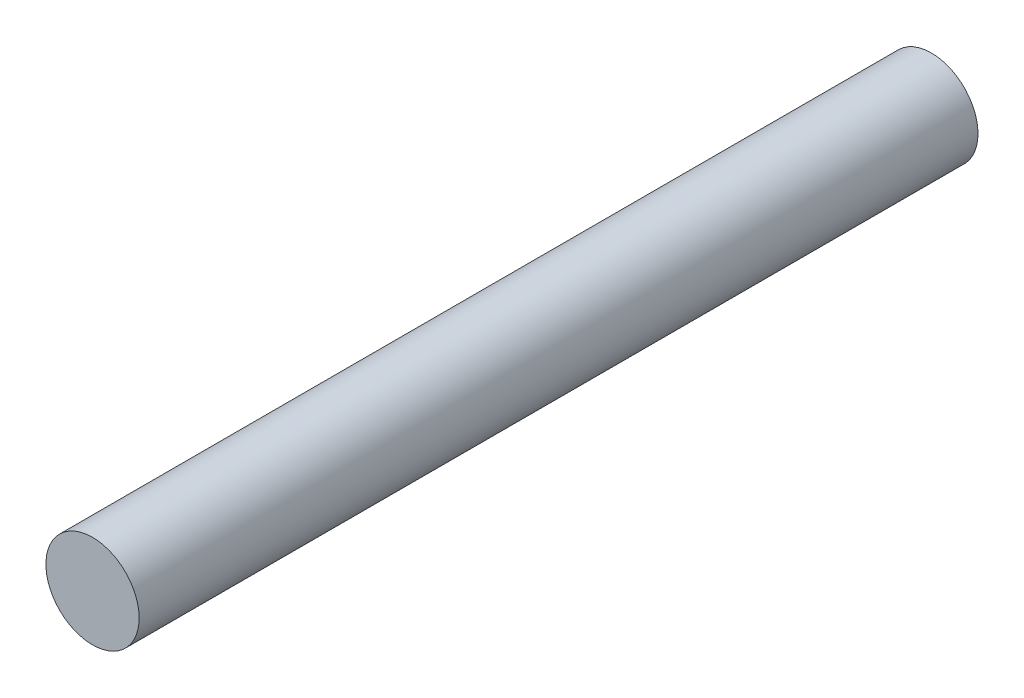
SolidWorks part; units mm, degrees
material "Acrylic (Medium-high impact)"
ref_plane "Front Plane" through (0, 0, 0) normal (0, 0, 1) x (1, 0, 0)
ref_plane "Top Plane" through (0, 0, 0) normal (0, 1, 0) x (1, 0, 0)
ref_plane "Right Plane" through (0, 0, 0) normal (1, 0, 0) x (0, 0, -1)
sketch "Sketch1" plane through (0, 0, 0) normal (0, 0, 1) x (1, 0, 0)
  circle A0 centre (0, 0) radius 1
  dimension "D1" = 2
extrude "Boss-Extrude1" add sketch "Sketch1" along normal blind 18
